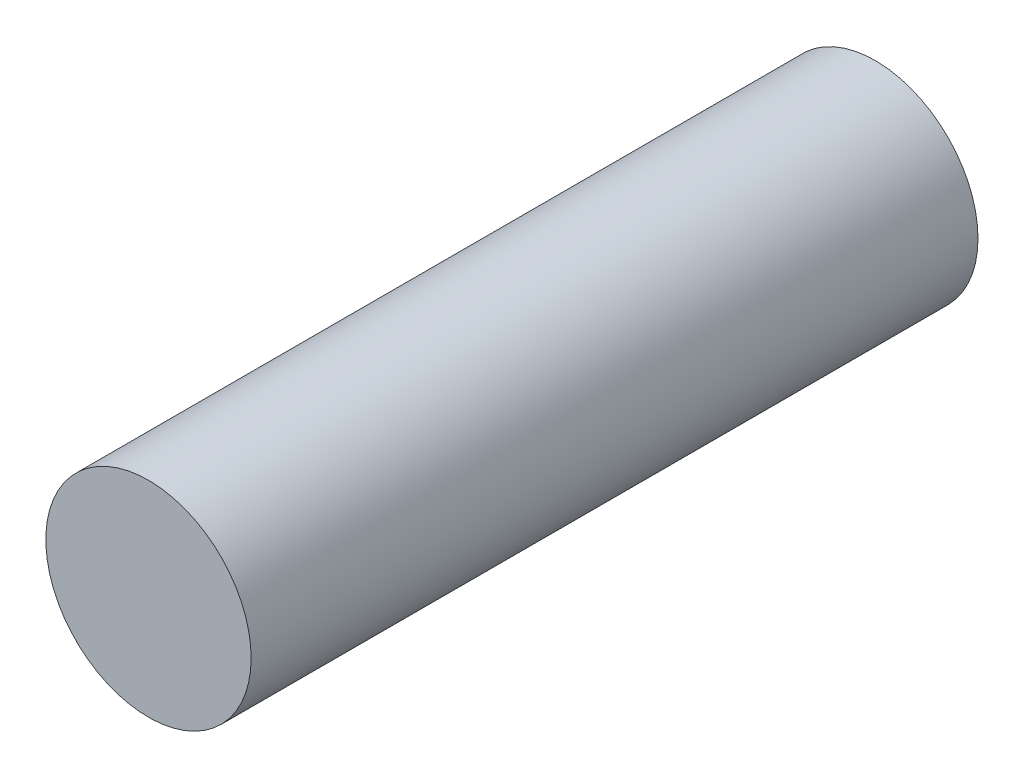
SolidWorks part; units mm, degrees
ref_plane "Front Plane" through (0, 0, 0) normal (0, 0, 1) x (1, 0, 0)
ref_plane "Top Plane" through (0, 0, 0) normal (0, 1, 0) x (1, 0, 0)
ref_plane "Right Plane" through (0, 0, 0) normal (1, 0, 0) x (0, 0, -1)
sketch "Sketch1" plane through (0, 0, 0) normal (0, 0, 1) x (1, 0, 0)
  circle A0 centre (0, 0) radius 9.25
  dimension "D1" = 18.5
extrude "Boss-Extrude1" add sketch "Sketch1" along normal blind 65.5
